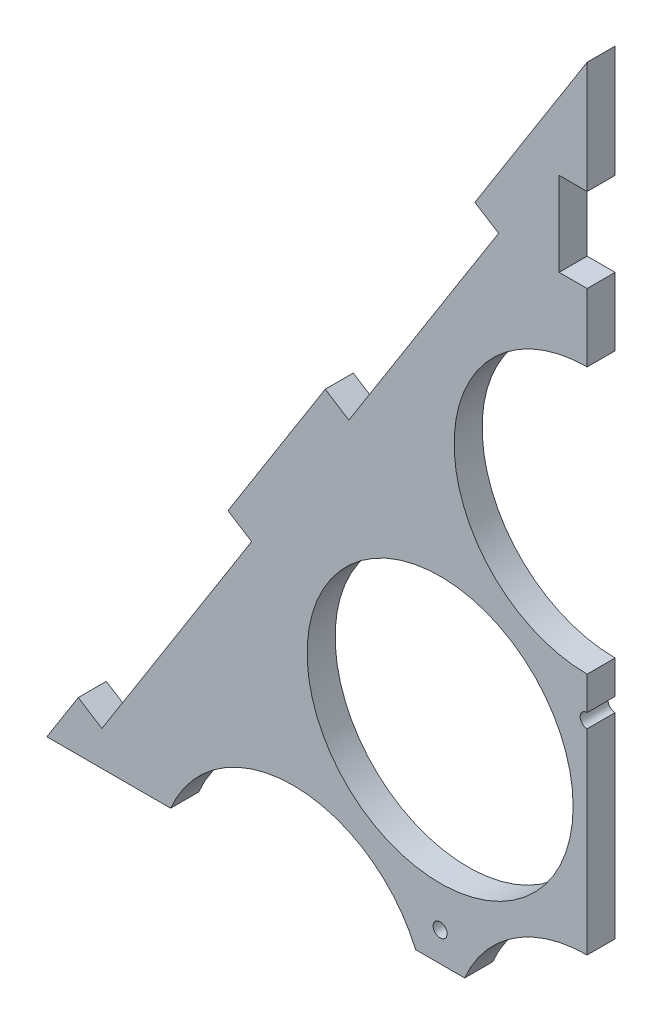
SolidWorks part; units mm, degrees
ref_plane "Plan de face" through (0, 0, 0) normal (0, 0, 1) x (1, 0, 0)
ref_plane "Plan de dessus" through (0, 0, 0) normal (0, 1, 0) x (1, 0, 0)
ref_plane "Plan de droite" through (0, 0, 0) normal (1, 0, 0) x (0, 0, -1)
sketch "Esquisse1" plane through (0, 0, 0) normal (0, 0, 1) x (1, 0, 0)
  line L0 (0, 0) -> (-371.1464, 0) construction
  line L1 (0, 0) -> (478.5179, 0) construction
  line L2 (0, 0) -> (0, 90.9327) construction
  line L3 (0, 90.9327) -> (-157.5, 90.9327) construction
  line L4 (0, 90.9327) -> (157.5, 90.9327) construction
  line L5 (0, 90.9327) -> (0, 181.8653) construction
  line L6 (0, 181.8653) -> (-52.5, 181.8653) construction
  line L7 (0, 181.8653) -> (52.5, 181.8653) construction
  line L8 (0, 181.8653) -> (0, 363.4062) construction
  line L9 (-310, -75.6429) -> (0, 414.5612)
  line L10 (0, 414.5612) -> (310, -75.6429)
  line L11 (310, -75.6429) -> (-310, -75.6429)
  circle A0 centre (-157.5, 0) radius 47.5
  circle A1 centre (-52.5, 0) radius 47.5
  circle A2 centre (52.5, 0) radius 47.5
  circle A3 centre (157.5, 0) radius 47.5
  circle A4 centre (-105, 90.9327) radius 47.5
  circle A5 centre (0, 90.9327) radius 47.5
  circle A6 centre (105, 90.9327) radius 47.5
  circle A7 centre (-52.5, 181.8653) radius 47.5
  circle A8 centre (52.5, 181.8653) radius 47.5
  circle A9 centre (0, 272.798) radius 47.5
  dimension "D1" = 95
  dimension "D2" = 95
  dimension "D3" = 95
  dimension "D4" = 95
  dimension "D5" = 105
  dimension "D6" = 52.5
  dimension "D7" = 52.5
  dimension "D8" = 105
  dimension "D9" = 95
  dimension "D10" = 95
  dimension "D11" = 95
  dimension "D12" = 105
  dimension "D13" = 105
  dimension "D14" = 105
  dimension "D15" = 95
  dimension "D16" = 95
  dimension "D17" = 105
  dimension "D18" = 52.5
  dimension "D19" = 52.5
  dimension "D20" = 95
  dimension "D21" = 105
  dimension "D22" = 80
  dimension "D23" = 620
  dimension "D24" = 580
  dimension "D25" = 0
  dimension "D26" = 580
extrude "Boss.-Extru.1" add sketch "Esquisse1" along normal blind 10
sketch "Esquisse3" plane through (0, 0, 10) normal (0, 0, 1) x (1, 0, 0)
  line L10 (-269.9138, -12.2544) -> (-261.462, -17.5992)
  line L15 (0, 414.5612) -> (-310, -75.6429) construction
  line L16 (-261.462, -17.5992) -> (-208.0137, 66.9187)
  line L17 (-208.0137, 66.9187) -> (-216.4655, 72.2635)
  line L18 (-216.4655, 72.2635) -> (-269.9138, -12.2544)
  line L19 (-181.7241, 127.2002) -> (-173.2723, 121.8554)
  line L20 (-173.2723, 121.8554) -> (-119.8241, 206.3733)
  line L21 (-119.8241, 206.3733) -> (-128.2759, 211.7181)
  line L22 (-128.2759, 211.7181) -> (-181.7241, 127.2002)
  line L23 (-93.5345, 266.6548) -> (-85.0827, 261.31)
  line L24 (-85.0827, 261.31) -> (-31.6344, 345.8279)
  line L25 (-31.6344, 345.8279) -> (-40.0862, 351.1727)
  line L26 (-40.0862, 351.1727) -> (-93.5345, 266.6548)
  line L27 (269.9138, -12.2544) -> (261.462, -17.5992)
  line L28 (310, -75.6429) -> (0, 414.5612) construction
  line L29 (261.462, -17.5992) -> (208.0137, 66.9187)
  line L30 (208.0137, 66.9187) -> (216.4655, 72.2635)
  line L31 (216.4655, 72.2635) -> (269.9138, -12.2544)
  line L32 (181.7241, 127.2002) -> (173.2723, 121.8554)
  line L33 (173.2723, 121.8554) -> (119.8241, 206.3733)
  line L34 (119.8241, 206.3733) -> (128.2759, 211.7181)
  line L35 (128.2759, 211.7181) -> (181.7241, 127.2002)
  line L36 (93.5345, 266.6548) -> (85.0827, 261.31)
  line L37 (85.0827, 261.31) -> (31.6344, 345.8279)
  line L38 (31.6344, 345.8279) -> (40.0862, 351.1727)
  line L39 (40.0862, 351.1727) -> (93.5345, 266.6548)
  line L40 (-310, -75.6429) -> (310, -75.6429) construction
  line L41 (-210, -75.6429) -> (-110, -75.6429)
  line L42 (-210, -75.6429) -> (-210, -65.6429)
  line L43 (-210, -65.6429) -> (-110, -65.6429)
  line L44 (-110, -75.6429) -> (-110, -65.6429)
  line L45 (0, 0) -> (0, -75.6429) construction
  line L46 (210, -65.6429) -> (110, -65.6429)
  line L47 (110, -75.6429) -> (110, -65.6429)
  line L48 (210, -75.6429) -> (110, -75.6429)
  line L49 (210, -75.6429) -> (210, -65.6429)
  dimension "D3" = 100
  dimension "D4" = 10
  dimension "D5" = 100
  dimension "D10" = 10
  dimension "D11" = 100
  dimension "D12" = 10
  dimension "D13" = 100
  dimension "D14" = 10
  dimension "D15" = 100
  dimension "D16" = 75
  dimension "D17" = 75
  dimension "D18" = 65
  dimension "D19" = 100
  dimension "D20" = 10
  dimension "D21" = 10
  dimension "D22" = 100
  dimension "D23" = 75
  dimension "D24" = 65
  dimension "D25" = 100
  dimension "D26" = 10
  dimension "D27" = 75
extrude "Enlèv. mat.-Extru.1" cut sketch "Esquisse3" against normal through all
sketch "Esquisse4" plane through (0, 0, 10) normal (0, 0, 1) x (1, 0, 0)
  line L0 (-110, -65.6429) -> (-210, -65.6429) construction
  circle A0 centre (-157.5, -55.6429) radius 2.5
  circle A3 centre (-52.5, -55.6429) radius 2.5
  circle A4 centre (52.5, -55.6429) radius 2.5
  circle A5 centre (157.5, -55.6429) radius 2.5
  circle A6 centre (-105, 29.0474) radius 2.5
  circle A8 centre (-157.5, 0) radius 47.5 construction
  circle A10 centre (-52.5, 0) radius 47.5 construction
  circle A12 centre (0, 29.0474) radius 2.5
  circle A13 centre (105, 29.0474) radius 2.5
  circle A14 centre (-52.5, 119.98) radius 2.5
  circle A15 centre (-105, 90.9327) radius 47.5 construction
  circle A16 centre (0, 90.9327) radius 47.5 construction
  circle A17 centre (52.5, 119.98) radius 2.5
  circle A18 centre (0, 210.9127) radius 2.5
  circle A19 centre (52.5, 181.8653) radius 47.5 construction
  circle A20 centre (-52.5, 181.8653) radius 47.5 construction
  dimension "D1" = 5
  dimension "D2" = 10
  dimension "D3" = 4
  dimension "D4" = 5
  dimension "D5" = 60
  dimension "D6" = 60
  dimension "D7" = 3
  dimension "D8" = 5
  dimension "D9" = 60
  dimension "D10" = 60
  dimension "D12" = 5
  dimension "D13" = 60
  dimension "D14" = 60
  dimension "D11" = 2
extrude "Enlèv. mat.-Extru.2" cut sketch "Esquisse4" against normal through all
sketch "Esquisse6" plane through (0, 0, 10) normal (0, 0, 1) x (1, 0, 0)
  line L0 (-110, -75.6429) -> (110, -75.6429) construction
  line L1 (-37.5, -75.6429) -> (37.5, -75.6429)
  line L2 (-37.5, -75.6429) -> (-37.5, -195.6429)
  line L3 (-37.5, -195.6429) -> (37.5, -195.6429)
  line L4 (37.5, -75.6429) -> (37.5, -195.6429)
  dimension "D1" = 75
  dimension "D2" = 120
  dimension "D3" = 37.5
extrude "Boss.-Extru.2" add sketch "Esquisse6" against normal blind 10
sketch "Esquisse7" plane through (0, 0, 10) normal (0, 0, 1) x (1, 0, 0)
  line L0 (-37.5, -75.6429) -> (-37.5, -195.6429) construction
  line L1 (-37.5, -110.6429) -> (-27.5, -110.6429)
  line L2 (-37.5, -110.6429) -> (-37.5, -160.6429)
  line L3 (-37.5, -160.6429) -> (-27.5, -160.6429)
  line L4 (-27.5, -110.6429) -> (-27.5, -160.6429)
  line L5 (-37.5, -195.6429) -> (37.5, -195.6429) construction
  line L6 (-13.5047, -195.6429) -> (16.4953, -195.6429)
  line L7 (-13.5047, -195.6429) -> (-13.5047, -186.0721)
  line L8 (-13.5047, -186.0721) -> (16.4953, -186.0721)
  line L9 (16.4953, -195.6429) -> (16.4953, -186.0721)
  line L10 (37.5, -195.6429) -> (37.5, -75.6429) construction
  line L11 (37.5, -160.6429) -> (27.5, -160.6429)
  line L12 (37.5, -160.6429) -> (37.5, -110.6429)
  line L13 (37.5, -110.6429) -> (27.5, -110.6429)
  line L14 (27.5, -160.6429) -> (27.5, -110.6429)
  line L15 (37.5, -75.6429) -> (110, -75.6429) construction
  line L16 (-110, -75.6429) -> (-37.5, -75.6429) construction
  dimension "D1" = 10
  dimension "D2" = 10
  dimension "D3" = 50
  dimension "D4" = 50
  dimension "D5" = 35
  dimension "D6" = 35
  dimension "D7" = 30
  dimension "D8" = 23.9953
extrude "Enlèv. mat.-Extru.3" cut sketch "Esquisse7" against normal blind 10
sketch "Esquisse11" plane through (0, 0, 10) normal (0, 0, 1) x (1, 0, 0)
  line L0 (0, 414.5612) -> (0, 109.4612)
  line L1 (0, 109.4612) -> (-346.1544, 109.4612)
  line L2 (-346.1544, 109.4612) -> (-346.1544, -222.5491)
  line L3 (-346.1544, -222.5491) -> (369.3465, -222.5491)
  line L4 (369.3465, -222.5491) -> (369.3465, 414.5612)
  line L5 (369.3465, 414.5612) -> (0, 414.5612)
  dimension "D1" = 305.1
extrude "Enlèv. mat.-Extru.6" cut sketch "Esquisse11" against normal blind 10
sketch "Esquisse12" plane through (0, 0, 10) normal (0, 0, 1) x (1, 0, 0)
  line L0 (0, 414.5612) -> (0, 320.298) construction
  line L1 (0, 374.5612) -> (-10, 374.5612)
  line L2 (0, 374.5612) -> (0, 344.5612)
  line L3 (0, 344.5612) -> (-10, 344.5612)
  line L4 (-10, 374.5612) -> (-10, 344.5612)
  dimension "D1" = 10
  dimension "D2" = 30
  dimension "D3" = 40
extrude "Enlèv. mat.-Extru.7" cut sketch "Esquisse12" against normal blind 10
